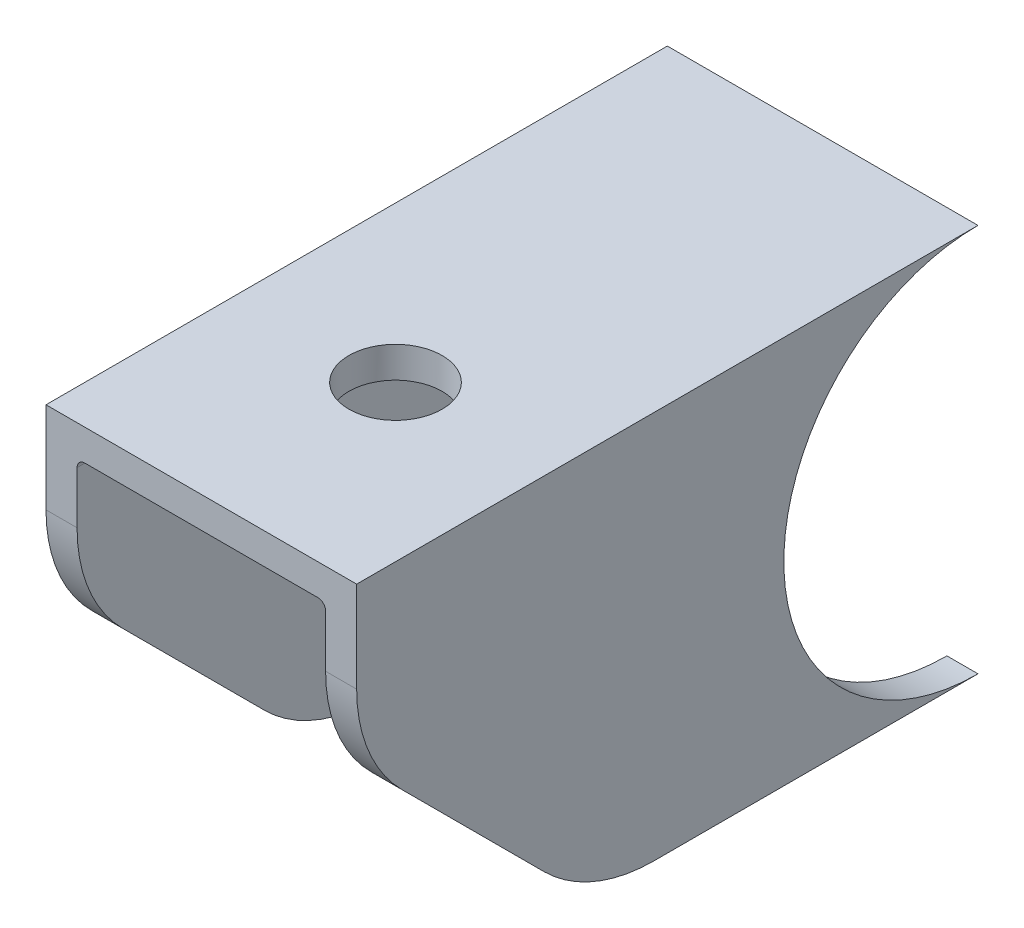
SolidWorks part; units mm, degrees
material "AISI 4130 Stal normalizowana w 870C"
ref_plane "Płaszczyzna XY" through (0, 0, 0) normal (0, 0, 1) x (1, 0, 0)
ref_plane "Płaszczyzna XZ" through (0, 0, 0) normal (0, 1, 0) x (1, 0, 0)
ref_plane "Płaszczyzna YZ" through (0, 0, 0) normal (1, 0, 0) x (0, 0, -1)
sketch "Szkic1" plane through (0, 0, 0) normal (1, 0, 0) x (0, 0, -1)
  line L1 (0, -25) -> (-20.8579, -25)
  line L3 (-40, 0) -> (0, 0)
  line L4 (-40, 0) -> (-40, -5.8579)
  line L5 (-37.0711, -12.9289) -> (-27.9289, -22.0711)
  arc A0 (-20.8579, -25) -> (-27.9289, -22.0711) centre (-20.8579, -15) cw
  arc A1 (-37.0711, -12.9289) -> (-40, -5.8579) centre (-30, -5.8579) cw
  arc A2 (0, 0) -> (0, -25) centre (0, -12.5) ccw
  point P8 (-25, -25)
  dimension "D5" = 10
  dimension "D6" = 12.5
  dimension "D1" = 135
  dimension "D2" = 25
  dimension "D3" = 40
  dimension "D4" = 25
extrude "Dodanie-wyciągnięcie1" add sketch "Szkic1" along normal mid plane 20
shell "Skorupa1" thickness 2
fillet "Zaokrąglenie1" radius 0.5 2 edges at (8, -2, 23.3912) (-8, -2, 23.3912)
sketch "Szkic2" plane through (0, 0, 0) normal (0, 1, 0) x (1, 0, 0)
  line L0 (10, 0) -> (10, -40) construction
  line L1 (10, -40) -> (-10, -40) construction
  circle A0 centre (0, -27.5) radius 3
  dimension "D1" = 10
  dimension "D4" = 12.5
  dimension "D5" = 6
extrude "Wytnij-wyciągnięcie1" cut sketch "Szkic2" against normal blind 10
